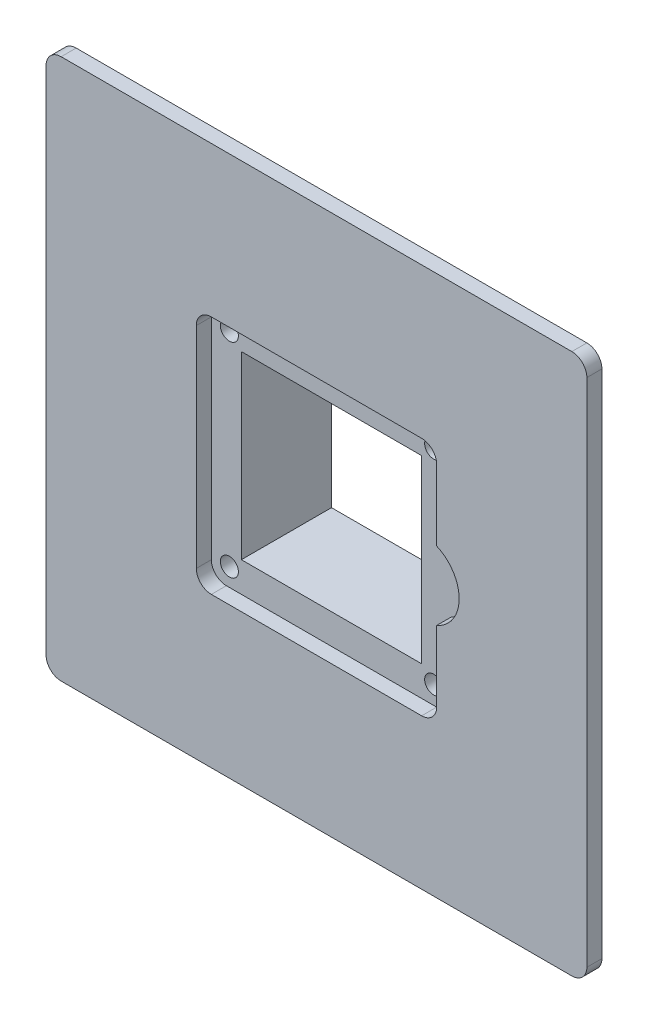
SolidWorks part; units mm, degrees
ref_plane "Front Plane" through (0, 0, 0) normal (0, 0, 1) x (1, 0, 0)
ref_plane "Top Plane" through (0, 0, 0) normal (0, 1, 0) x (1, 0, 0)
ref_plane "Right Plane" through (0, 0, 0) normal (1, 0, 0) x (0, 0, -1)
sketch "Sketch1" plane through (0, 0, 0) normal (0, 0, 1) x (1, 0, 0)
  line L1 (0, 0) -> (90, 0)
  line L2 (0, 0) -> (0, 90)
  line L3 (0, 90) -> (90, 90)
  line L4 (90, 0) -> (90, 90)
  dimension "D1" = 90
  dimension "D2" = 90
extrude "Boss-Extrude1" add sketch "Sketch1" along normal blind 2.5
sketch "Sketch2" plane through (0, 0, 2.5) normal (0, 0, 1) x (1, 0, 0)
  line L0 (90, 45) -> (0, 45) construction
  line L1 (90, 0) -> (90, 90) construction
  line L2 (45, 90) -> (45, 0) construction
  line L3 (0, 0) -> (90, 0) construction
  line L4 (90, 90) -> (0, 90) construction
  line L5 (25, 65) -> (65, 65)
  line L6 (25, 65) -> (25, 25)
  line L7 (25, 25) -> (65, 25)
  line L8 (65, 65) -> (65, 25)
  line L9 (0, 90) -> (0, 0) construction
  dimension "D2" = 20
  dimension "D3" = 20
  dimension "D13" = 40
  dimension "D14" = 40
sketch "Sketch3" plane through (0, 0, 0) normal (0, 0, -1) x (-1, 0, 0)
  line L1 (-70, 70) -> (-20, 70)
  line L2 (-70, 70) -> (-70, 20)
  line L3 (-70, 20) -> (-20, 20)
  line L4 (-20, 70) -> (-20, 20)
  line L6 (-45, 90) -> (-45, 0) construction
  line L7 (-90, 90) -> (0, 90) construction
  line L8 (0, 0) -> (-90, 0) construction
  line L9 (-90, 45) -> (0, 45) construction
  line L10 (-90, 0) -> (-90, 90) construction
  line L11 (0, 90) -> (0, 0) construction
  dimension "D1" = 50
  dimension "D2" = 50
  dimension "D3" = 25
  dimension "D4" = 25
extrude "Boss-Extrude4" add sketch "Sketch3" along normal blind 15
extrude "Cut-Extrude4" cut sketch "Sketch2" against normal blind 2.5
sketch "Sketch8" plane through (0, 0, 0) normal (0, 0, 1) x (1, 0, 0)
  line L0 (65, 25) -> (65, 65) construction
  line L1 (65, 65) -> (25, 65) construction
  line L2 (25, 65) -> (25, 25) construction
  line L3 (25, 25) -> (65, 25) construction
  line L4 (25, 65) -> (25, 25) construction
  line L6 (65, 25) -> (65, 65) construction
  circle A0 centre (62, 62) radius 1.5
  circle A1 centre (62, 28) radius 1.5
  circle A2 centre (28, 62) radius 1.5
  circle A3 centre (28, 28) radius 1.5
  dimension "D1" = 3
  dimension "D4" = 3
  dimension "D5" = 3
  dimension "D6" = 3
  dimension "D2" = 3
  dimension "D3" = 3
  dimension "D7" = 3
  dimension "D8" = 3
  dimension "D9" = 3
  dimension "D10" = 3
  dimension "D11" = 3
  dimension "D12" = 3
extrude "Cut-Extrude6" cut sketch "Sketch8" against normal blind 5
fillet "Fillet1" radius 2.5 4 edges at (0, 0, 1.25) (90, 0, 1.25) (0, 90, 1.25) (90, 90, 1.25)
fillet "Fillet2" radius 2.5 2 edges at (25, 65, 1.25) (65, 65, 1.25)
fillet "Fillet3" radius 2.5 2 edges at (25, 25, 1.25) (65, 25, 1.25)
sketch "Sketch10" plane through (0, 0, 2.5) normal (0, 0, 1) x (1, 0, 0)
  line L0 (90, 45) -> (0, 45) construction
  line L1 (90, 2.5) -> (90, 87.5) construction
  line L2 (0, 87.5) -> (0, 2.5) construction
  line L3 (2.5, 0) -> (87.5, 0) construction
  line L4 (65, 27.5) -> (65, 62.5) construction
  circle A1 centre (62.5, 45) radius 6.25
  dimension "D1" = 2.5
  dimension "D2" = 12.5
  dimension "D3" = 45
extrude "Cut-Extrude12" cut sketch "Sketch10" against normal blind 2.5
sketch "Sketch11" plane through (0, 0, 0) normal (0, 0, 1) x (1, 0, 0)
  line L0 (45, 25) -> (45, 65) construction
  line L1 (60, 30) -> (30, 30)
  line L2 (60, 30) -> (60, 60)
  line L3 (60, 60) -> (30, 60)
  line L4 (30, 30) -> (30, 60)
  line L5 (27.5, 25) -> (62.5, 25) construction
  line L6 (62.5, 65) -> (27.5, 65) construction
  line L7 (25, 45) -> (68.75, 45) construction
  line L8 (25, 62.5) -> (25, 27.5) construction
  arc A0 (65, 39.2718) -> (65, 50.7282) centre (62.5, 45) ccw construction
  dimension "D1" = 15
  dimension "D2" = 15
  dimension "D3" = 15
  dimension "D4" = 15
extrude "Cut-Extrude13" cut sketch "Sketch11" against normal up to surface (15 mm away) up to face at (45, 45, -15)
sketch "Sketch12" plane through (0, 0, -15) normal (0, 0, -1) x (-1, 0, 0)
  line L0 (-20, 45) -> (-70, 45) construction
  line L1 (-20, 20) -> (-20, 70) construction
  line L2 (-70, 70) -> (-70, 20) construction
  line L3 (-45, 20) -> (-45, 70) construction
  line L4 (-70, 20) -> (-20, 20) construction
  line L5 (-20, 70) -> (-70, 70) construction
  circle A0 centre (-28, 28) radius 1.5
  circle A1 centre (-28, 62) radius 1.5
  circle A2 centre (-62, 62) radius 1.5
  circle A3 centre (-62, 28) radius 1.5
  point P20 (0, 0)
  dimension "D2" = 3
  dimension "D3" = 3
  dimension "D4" = 3
  dimension "D5" = 3
  dimension "D6" = 17
  dimension "D1" = 17
  dimension "D7" = 17
  dimension "D8" = 17
  dimension "D9" = 17
  dimension "D10" = 17
  dimension "D11" = 17
  dimension "D12" = 17
extrude "Cut-Extrude14" cut sketch "Sketch12" against normal blind 5
fillet "Fillet4" radius 5 2 edges at (70, 20, -7.5) (70, 70, -7.5)
fillet "Fillet5" radius 5 2 edges at (20, 20, -7.5) (20, 70, -7.5)
